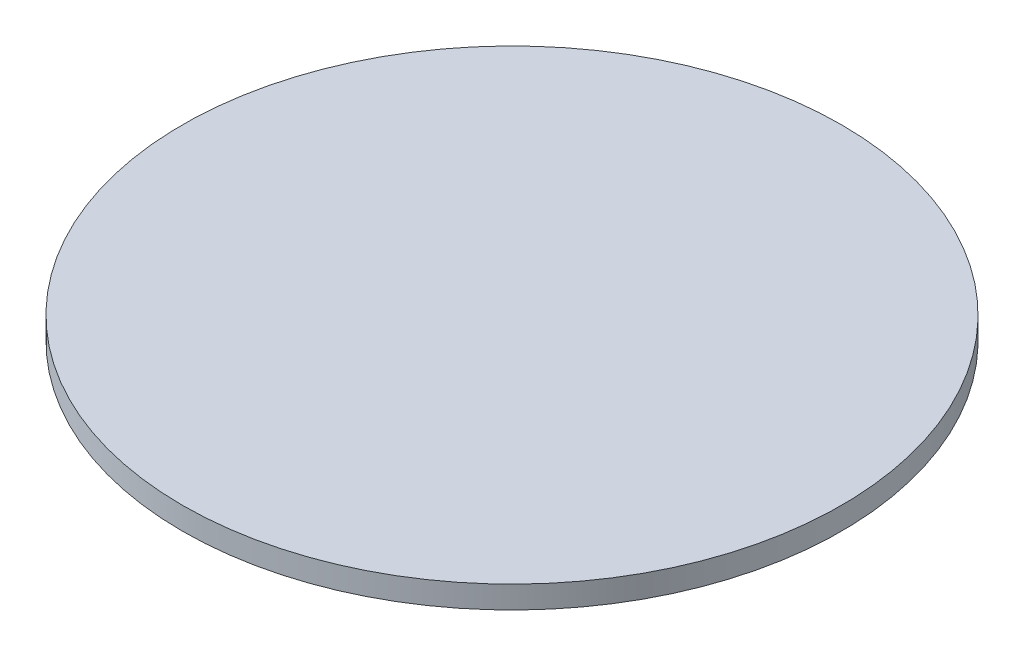
SolidWorks part; units mm, degrees
ref_plane "Front Plane" through (0, 0, 0) normal (0, 0, 1) x (1, 0, 0)
ref_plane "Top Plane" through (0, 0, 0) normal (0, 1, 0) x (1, 0, 0)
ref_plane "Right Plane" through (0, 0, 0) normal (1, 0, 0) x (0, 0, -1)
sketch "Sketch1" plane through (0, 0, 0) normal (0, 1, 0) x (1, 0, 0)
  circle A0 centre (0, 0) radius 11.75
  dimension "D1" = 23.5
extrude "Boss-Extrude1" add sketch "Sketch1" along normal blind 0.8 contours A0
